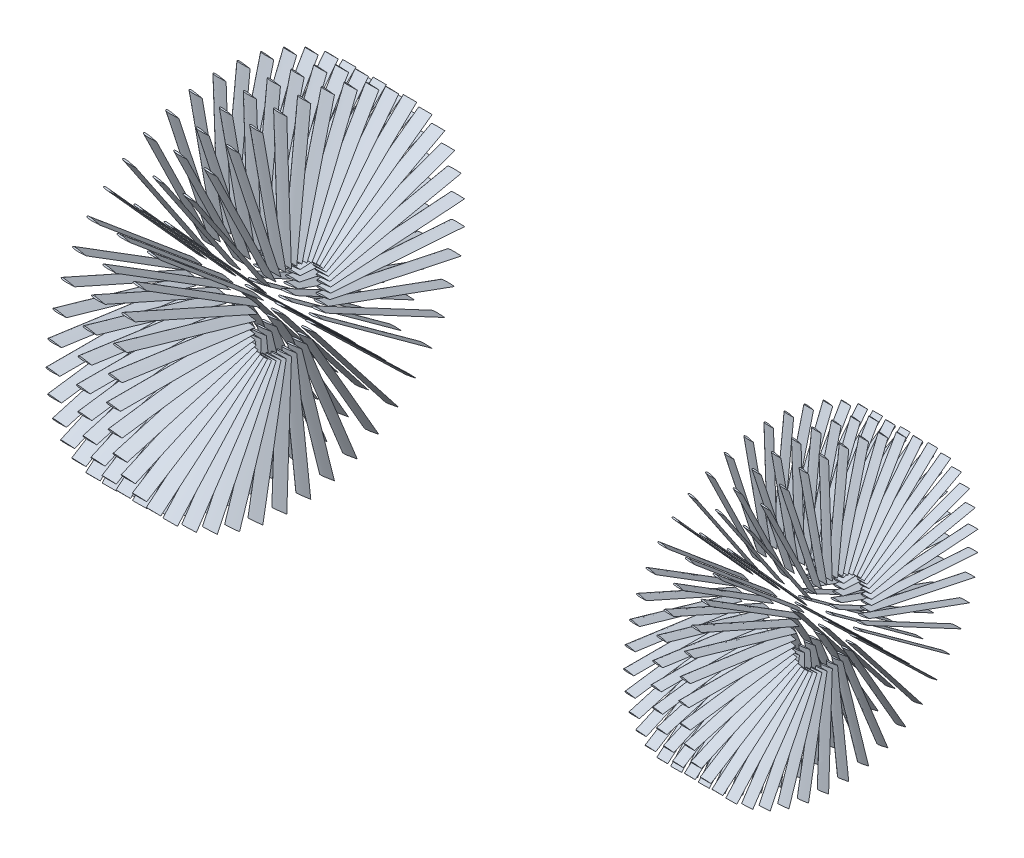
SolidWorks part; units mm, degrees
ref_plane "Front Plane" through (0, 0, 0) normal (0, 0, 1) x (1, 0, 0)
ref_plane "Top Plane" through (0, 0, 0) normal (0, 1, 0) x (1, 0, 0)
ref_plane "Right Plane" through (0, 0, 0) normal (1, 0, 0) x (0, 0, -1)
sketch "Sketch1" plane through (0, 0, 0) normal (0, 0, 1) x (1, 0, 0)
  line L0 (0, 0) -> (14.9603, 0) construction
  line L1 (14.9603, 0) -> (389.017, 0) construction
  spline S0 degree 2 poles (0.0364, 0.8522) (0.7068, 1.6116) (10, 0) knots 0 0 0 1 1 1
  spline S1 degree 2 poles (0.0364, 0.8522) (-1.0038, -0.6229) (10, 0) knots 0 0 0 1 1 1
  spline S2 degree 2 poles (354.9994, 0.6534) (355.3252, 1.7621) (362.4711, 0.0025) knots 0 0 0 1 1 1
  spline S3 degree 2 poles (354.9994, 0.6534) (354.8203, -0.2233) (362.4711, 0.0025) knots 0 0 0 1 1 1
  dimension "D1" = 10
  dimension "D2" = 2.026
  dimension "D3" = 3.61
  dimension "D7" = 10
  dimension "D8" = 0.6534
  dimension "D4" = 345
  dimension "D5" = 7.5
  dimension "D6" = 0
  dimension "D9" = 0.0025
extrude "Boss-Extrude3" add sketch "Sketch1" along normal blind 97.5
sketch "Sketch6" plane through (0, 0, 97.5) normal (0, 0, 1) x (1, 0, 0)
  circle A0 centre (362.4711, 0.0025) radius 7.868
extrude "Cut-Extrude1" cut sketch "Sketch6" against normal blind 20
sketch "Sketch7" plane through (0, 0, 0) normal (1, 0, 0) x (0, 0, -1)
  line L0 (0, 0) -> (27.5, 0)
  dimension "D1" = 27.5
sketch "Sketch8" plane through (0, 0, 0) normal (0, 1, 0) x (1, 0, 0)
  line L0 (-186.3522, 27.5) -> (633.9798, 27.5) construction
pattern_circular "CirPattern4" count 45 over 360 about axis through (-186.3522, 0, -27.5) along (1, 0, 0)
pattern_linear "LPattern1" count 3 spacing 22 along (1, 0, 0)
pattern_linear "LPattern2" count 3 spacing 20 along (1, 0, 0) of bodies 113 126 139 115 128 141 117 130 143 106 119 132 145 108 121 134 147 110 123 136 105 149 112 125 138 114 127 140 116 129 142 118 131 144 107 120 133 146 109 122
